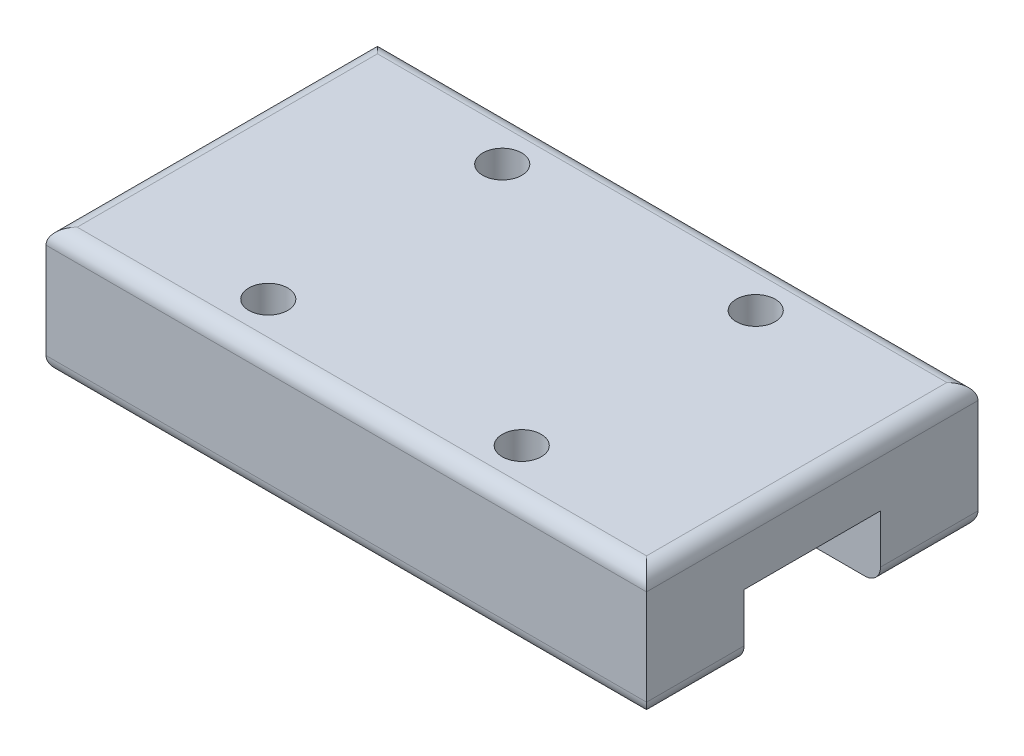
SolidWorks part; units mm, degrees
material "ABS"
ref_plane "前视基准面" through (0, 0, 0) normal (0, 0, 1) x (1, 0, 0)
ref_plane "上视基准面" through (0, 0, 0) normal (0, 1, 0) x (1, 0, 0)
ref_plane "右视基准面" through (0, 0, 0) normal (1, 0, 0) x (0, 0, -1)
sketch "草图1" plane through (0, 0, 0) normal (0, 0, 1) x (1, 0, 0)
  line L0 (-63.7855, 0) -> (80.5132, 0) construction
  line L1 (0, 47.6734) -> (0, -63.3818) construction
  line L3 (-15.4, 3.25) -> (15.4, 3.25)
  line L4 (-15.4, 3.25) -> (-15.4, -3.25)
  line L5 (-15.4, -3.25) -> (15.4, -3.25)
  line L6 (15.4, 3.25) -> (15.4, -3.25)
  dimension "D1" = 6.5
  dimension "D2" = 3.25
  dimension "D3" = 30.8
  dimension "D4" = 15.4
extrude "凸台-拉伸1" add sketch "草图1" along normal mid plane 17
sketch "草图2" plane through (0, 3.25, 0) normal (0, 1, 0) x (1, 0, 0)
  line L0 (0, 8.5) -> (0, -8.5) construction
  line L1 (15.4, 8.5) -> (-15.4, 8.5) construction
  line L2 (15.4, -8.5) -> (-15.4, -8.5) construction
  line L3 (-15.4, 0) -> (15.4, 0) construction
  line L4 (-15.4, -8.5) -> (-15.4, 8.5) construction
  line L5 (15.4, -8.5) -> (15.4, 8.5) construction
  circle A0 centre (-6.5, 6) radius 1
  circle A1 centre (-6.5, -6) radius 1
  circle A2 centre (6.5, 6) radius 1
  circle A3 centre (6.5, -6) radius 1
  dimension "D1" = 2
  dimension "D2" = 2
  dimension "D3" = 2
  dimension "D4" = 2
  dimension "D6" = 6.5
  dimension "D7" = 13
  dimension "D5" = 13
  dimension "D8" = 6.5
  dimension "D9" = 12
  dimension "D10" = 6
extrude "切除-拉伸1" cut sketch "草图2" against normal blind 2.5
sketch "草图3" plane through (-15.4, 0, 0) normal (-1, 0, 0) x (0, 0, 1)
  line L0 (-3.5, -3.25) -> (-3.5, 0.05)
  line L1 (8.5, -3.25) -> (-8.5, -3.25) construction
  line L2 (-3.5, 0.05) -> (3.5, 0.05)
  line L3 (3.5, 0.05) -> (3.5, -3.25)
  line L4 (3.5, -3.25) -> (-3.5, -3.25)
  line L5 (-8.5, 3.25) -> (-8.5, -3.25) construction
  line L6 (8.5, 3.25) -> (8.5, -3.25) construction
  dimension "D1" = 3.3
  dimension "D2" = 5
  dimension "D3" = 5
extrude "切除-拉伸2" cut sketch "草图3" against normal up to next
fillet "圆角1" radius 0.8 10 edges at (15.4, -3.25, 6) (-15.4, -3.25, -6) (0, -3.25, -8.5) (15.4, -3.25, -6) (-15.4, -3.25, 6) (0, -3.25, 8.5) (0, 3.25, -8.5) (15.4, 3.25, 0) (0, 3.25, 8.5) (-15.4, 3.25, 0)
